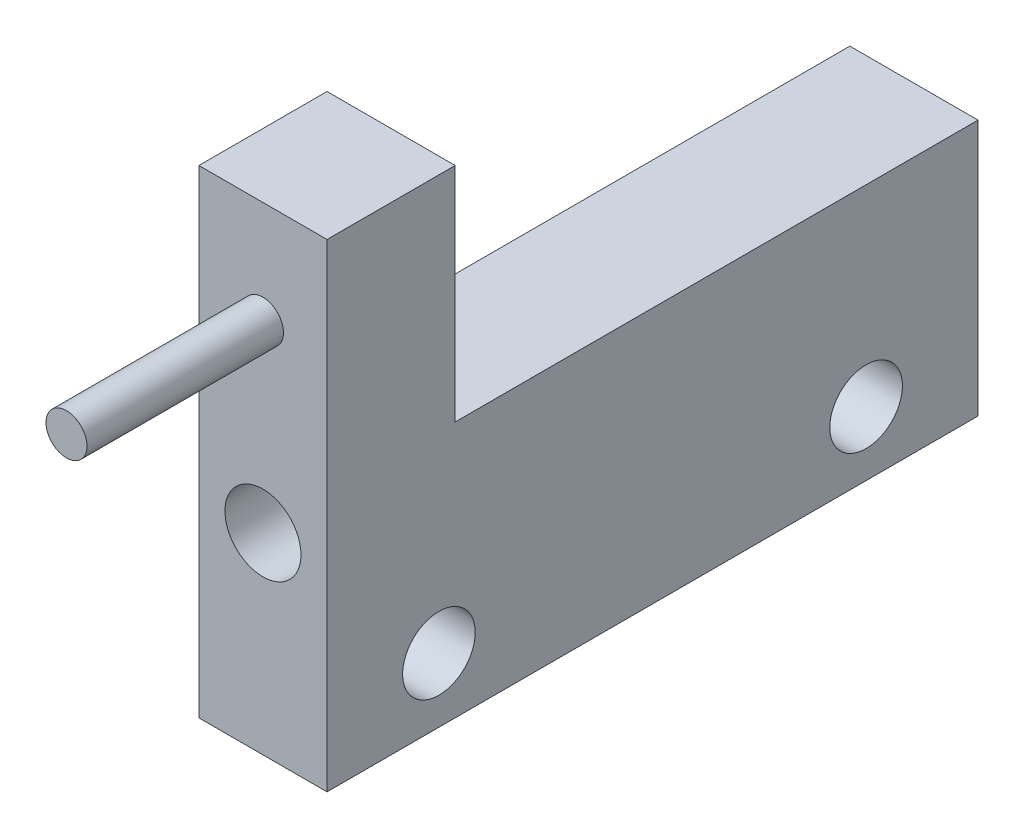
SolidWorks part; units mm, degrees
ref_plane "Front Plane" through (0, 0, 0) normal (0, 0, 1) x (1, 0, 0)
ref_plane "Top Plane" through (0, 0, 0) normal (0, 1, 0) x (1, 0, 0)
ref_plane "Right Plane" through (0, 0, 0) normal (1, 0, 0) x (0, 0, -1)
sketch "Sketch2" plane through (0, 0, 0) normal (0, 0, 1) x (1, 0, 0)
  line L0 (-10.954, 39.1928) -> (-10.954, 9.1928) construction
  line L1 (-18.454, 39.1928) -> (-3.454, 39.1928)
  line L2 (-18.454, 39.1928) -> (-18.454, 9.1928)
  line L3 (-18.454, 9.1928) -> (-3.454, 9.1928)
  line L4 (-3.454, 39.1928) -> (-3.454, 9.1928)
  line L5 (-10.954, 24.1928) -> (-3.454, 24.1928) construction
  circle A0 centre (-10.954, 31.6928) radius 4.45
  dimension "D3" = 8.9
  dimension "D4" = 7.5
  dimension "D1" = 15
  dimension "D2" = 30
extrude "Boss-Extrude1" add sketch "Sketch2" along normal blind 76.2
sketch "Sketch3" plane through (-3.454, 0, 0) normal (1, 0, 0) x (0, 0, -1)
  line L0 (-76.2, 24.1928) -> (0, 24.1928) construction
  line L1 (-76.2, 9.1928) -> (-76.2, 39.1928) construction
  line L2 (0, 9.1928) -> (0, 39.1928) construction
  line L3 (-38.1, 24.1928) -> (-38.1, 9.1928) construction
  line L4 (-76.2, 9.1928) -> (0, 9.1928) construction
  line L5 (-38.1, 16.6928) -> (-76.2, 16.6928) construction
  circle A0 centre (-63.1, 16.6928) radius 4.25
  circle A1 centre (-13.1, 16.6928) radius 4.25
  dimension "D1" = 8.5
  dimension "D2" = 50
  dimension "D3" = 76.2
extrude "Cut-Extrude2" cut sketch "Sketch3" against normal through all
sketch "Sketch5" plane through (0, 0, 76.2) normal (0, 0, 1) x (1, 0, 0)
  line L0 (-18.454, 39.1928) -> (-18.454, 9.1928) construction
  line L1 (-3.454, 39.1928) -> (-18.454, 39.1928)
  line L2 (-3.454, 39.1928) -> (-3.454, 65.1928)
  line L3 (-3.454, 65.1928) -> (-18.454, 65.1928)
  line L4 (-18.454, 39.1928) -> (-18.454, 65.1928)
  line L5 (-3.454, 9.1928) -> (-3.454, 39.1928) construction
  line L6 (-10.954, 39.1928) -> (-10.954, 65.1928) construction
  circle A0 centre (-10.954, 52.1928) radius 2.3
  dimension "D3" = 4.6
  dimension "D1" = 13
  dimension "D2" = 13
extrude "Boss-Extrude3" add sketch "Sketch5" against normal blind 15 contours L2 L1 L4 L3
sketch "Sketch8" plane through (0, 0, 76.2) normal (0, 0, 1) x (1, 0, 0)
  line L0 (-10.954, 65.1928) -> (-10.954, 53.1928) construction
  line L1 (-3.454, 65.1928) -> (-18.454, 65.1928) construction
  circle A0 centre (-10.954, 53.1928) radius 2.4
  dimension "D2" = 4.8
  dimension "D1" = 12
extrude "Boss-Extrude4" add sketch "Sketch8" along normal blind 23
sketch "Sketch9" plane through (0, 0, 76.2) normal (0, 0, 1) x (1, 0, 0)
  line L0 (-18.454, 65.1928) -> (-18.454, 9.1928) construction
  line L1 (-18.454, 9.1928) -> (-3.454, 9.1928) construction
  line L2 (-3.454, 9.1928) -> (-3.454, 65.1928) construction
  line L3 (-3.454, 65.1928) -> (-18.454, 65.1928) construction
  line L4 (-18.454, 65.1928) -> (-18.454, 9.1928)
  line L5 (-18.454, 9.1928) -> (-3.454, 9.1928)
  line L6 (-3.454, 9.1928) -> (-3.454, 65.1928)
  line L7 (-3.454, 65.1928) -> (-18.454, 65.1928)
  circle A0 centre (-10.954, 53.1928) radius 2.4 construction
  circle A1 centre (-10.954, 53.1928) radius 2.4
  dimension "D1" = 44
